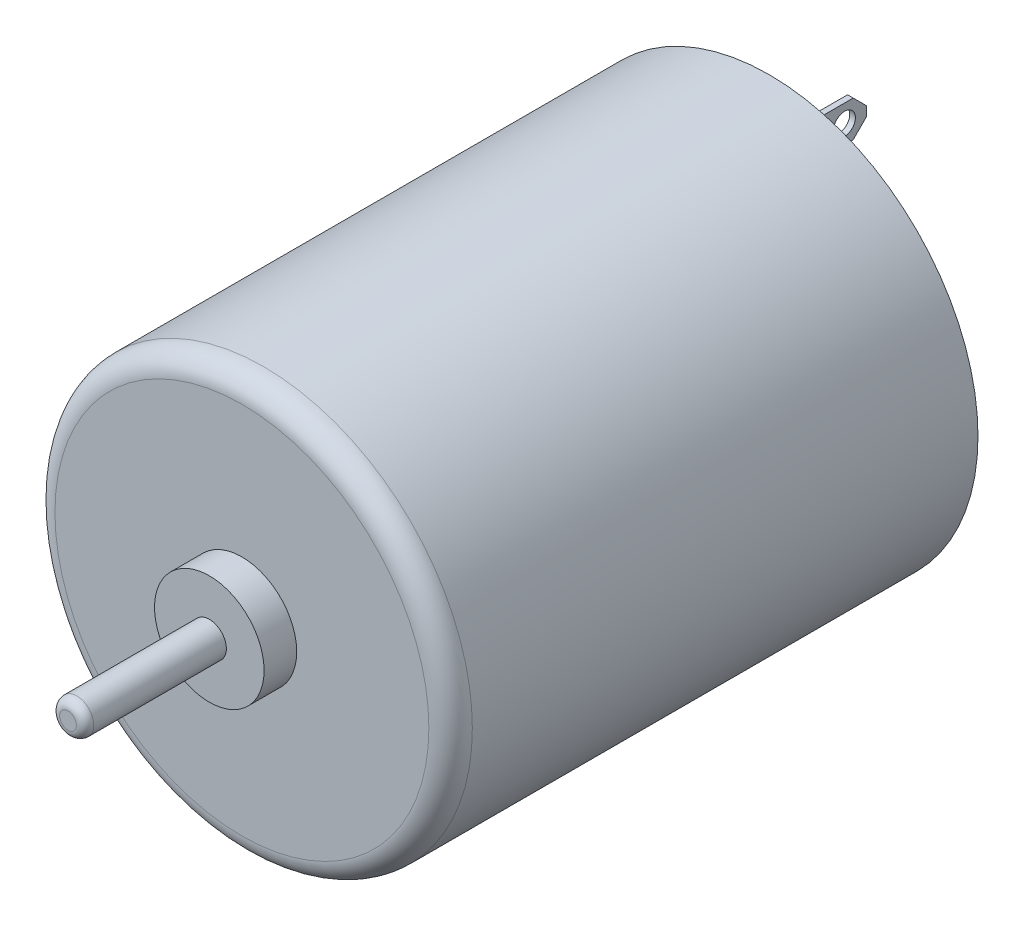
SolidWorks part; units mm, degrees
ref_plane "Front Plane" through (0, 0, 0) normal (0, 0, 1) x (1, 0, 0)
ref_plane "Top Plane" through (0, 0, 0) normal (0, 1, 0) x (1, 0, 0)
ref_plane "Right Plane" through (0, 0, 0) normal (1, 0, 0) x (0, 0, -1)
sketch "Sketch1" plane through (0, 0, 0) normal (0, 0, 1) x (1, 0, 0)
  circle A0 centre (0, 0) radius 12.192
  dimension "D1" = 24.384
extrude "Boss-Extrude1" add sketch "Sketch1" along normal blind 30.8102
sketch "Sketch2" plane through (0, 0, 30.8102) normal (0, 0, 1) x (1, 0, 0)
  circle A0 centre (0, 0) radius 0.9969
  dimension "D1" = 1.9939
extrude "Boss-Extrude3" add sketch "Sketch2" along normal blind 10.16 contours A0
sketch "Sketch6" plane through (0, 0, 30.8102) normal (0, 0, 1) x (1, 0, 0)
  circle A0 centre (0, 0) radius 3.2004
  dimension "D1" = 6.4008
extrude "Boss-Extrude4" add sketch "Sketch6" along normal blind 1.905
fillet "Fillet2" radius 0.508 1 edges at (0.9969, 0, 40.9702)
fillet "Fillet3" radius 1.27 1 edges at (12.192, 0, 30.8102)
sketch "Sketch7" plane through (0, 0, 0) normal (0, 0, -1) x (-1, 0, 0)
  circle A0 centre (0, 0) radius 11.7094
  circle A1 centre (0, 0) radius 12.192 construction
  dimension "D1" = 0.4826
extrude "Cut-Extrude1" cut sketch "Sketch7" against normal blind 1.016
sketch "Sketch10" plane through (0, 0, 1.016) normal (0, 0, -1) x (-1, 0, 0)
  circle A0 centre (0, 0) radius 3.2258
  dimension "D1" = 6.4516
extrude "Boss-Extrude5" add sketch "Sketch10" along normal blind 2.794
fillet "Fillet4" radius 0.889 1 edges at (-3.2258, 0, -1.778)
sketch "Sketch11" plane through (0, 0, 1.016) normal (0, 0, -1) x (-1, 0, 0)
  line L1 (1.27, -8.0518) -> (1.6002, -8.0518)
  line L2 (1.27, -8.0518) -> (1.27, -10.16)
  line L3 (1.27, -10.16) -> (1.6002, -10.16)
  line L4 (1.6002, -8.0518) -> (1.6002, -10.16)
  circle A0 centre (0, 0) radius 2.3368 construction
  dimension "D1" = 1.27
  dimension "D2" = 0.3302
  dimension "D3" = 2.1082
  dimension "D4" = 10.16
extrude "Boss-Extrude6" add sketch "Sketch11" along normal blind 5.08
sketch "Sketch12" plane through (-1.27, 0, 0) normal (1, 0, 0) x (0, 0, -1)
  line L0 (3.302, -8.0518) -> (4.064, -8.8138)
  line L1 (4.064, -8.0518) -> (-1.016, -8.0518) construction
  line L2 (4.064, -8.0518) -> (4.064, -10.16) construction
  line L3 (4.064, -9.398) -> (3.302, -10.16)
  line L4 (4.064, -10.16) -> (-1.016, -10.16) construction
  line L6 (3.302, -8.0518) -> (4.064, -8.0518)
  line L7 (4.064, -8.0518) -> (4.064, -8.8138)
  line L8 (3.302, -10.16) -> (4.064, -10.16)
  line L9 (4.064, -10.16) -> (4.064, -9.398)
  circle A0 centre (2.794, -9.1059) radius 0.635
  dimension "D6" = 1.27
  dimension "D1" = 0.762
  dimension "D2" = 0.762
  dimension "D3" = 0.762
  dimension "D4" = 0.762
  dimension "D5" = 1.27
  dimension "D7" = 1.0541
extrude "Cut-Extrude2" cut sketch "Sketch12" against normal up to next (0.3302 mm away)
pattern_circular "CirPattern1" count 2 over 360 about axis through (0, 0, 0) along (0, 0, 1) of "Cut-Extrude2", "Boss-Extrude6"
